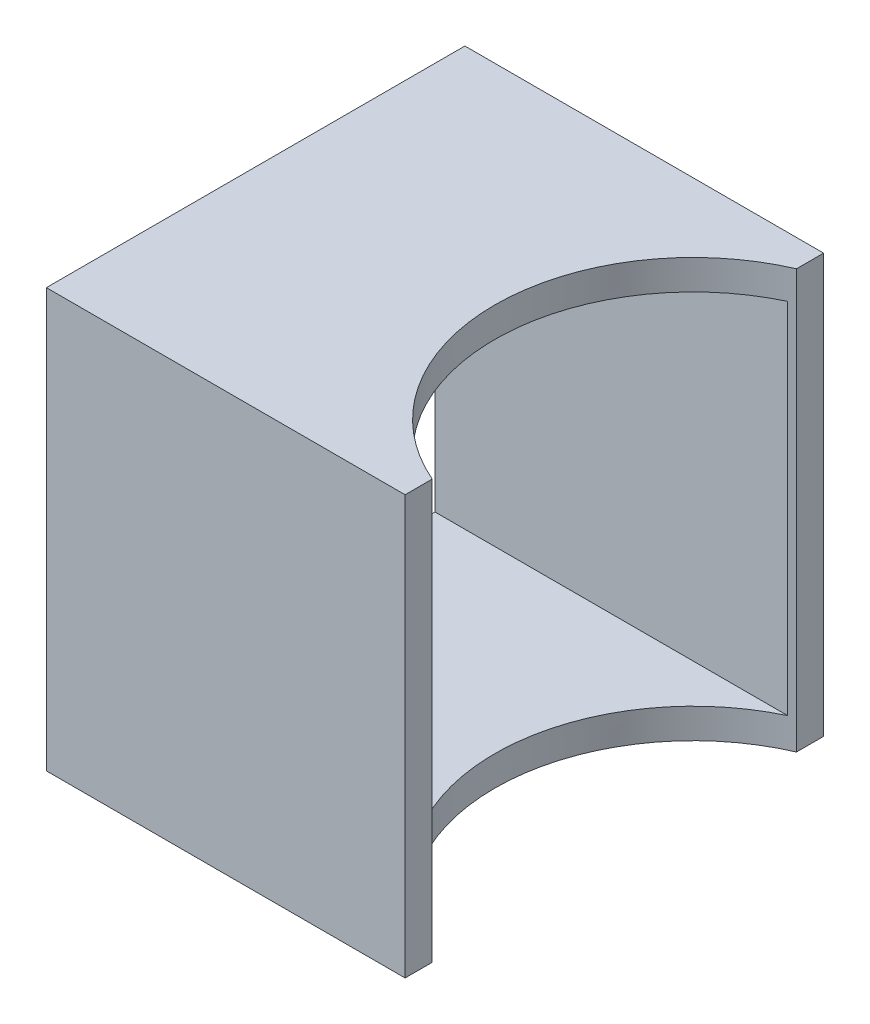
SolidWorks part; units mm, degrees
material "6061 Alloy"
ref_plane "Front Plane" through (0, 0, 0) normal (0, 0, 1) x (1, 0, 0)
ref_plane "Top Plane" through (0, 0, 0) normal (0, 1, 0) x (1, 0, 0)
ref_plane "Right Plane" through (0, 0, 0) normal (1, 0, 0) x (0, 0, -1)
sketch "Sketch1" plane through (0, 0, 0) normal (0, 1, 0) x (1, 0, 0)
  line L0 (0, 0) -> (46.482, 0) construction
  line L1 (0, -22.225) -> (0, 22.225)
  line L2 (0, 22.225) -> (38.1, 22.225)
  line L3 (38.1, 22.225) -> (38.1, 19.3441)
  line L4 (0, -22.225) -> (38.1, -22.225)
  line L5 (38.1, -22.225) -> (38.1, -19.3441)
  circle A0 centre (46.482, 0) radius 21.082
  dimension "D1" = 42.164
  dimension "D2" = 46.482
  dimension "D3" = 44.45
  dimension "D4" = 2.8809
  dimension "D5" = 38.1
extrude "Boss-Extrude1" add sketch "Sketch1" along normal blind 44.45 contours L0 L1 L4 L5 A0 | L1 L0 A0 L3 L2
sketch "Sketch2" plane through (0, 0, 0) normal (-1, 0, 0) x (0, 0, 1)
  line L0 (22.225, 44.45) -> (22.225, 0) construction
  line L1 (-22.225, 44.45) -> (22.225, 44.45) construction
  line L2 (-22.225, 44.45) -> (-22.225, 0) construction
  line L3 (-22.225, 0) -> (22.225, 0) construction
  line L4 (22.225, 44.45) -> (22.225, 0) construction
  line L5 (-19.05, 41.275) -> (-19.05, 3.175)
  line L6 (-19.05, 3.175) -> (19.05, 3.175)
  line L7 (19.05, 41.275) -> (19.05, 3.175)
  line L8 (-19.05, 41.275) -> (19.05, 41.275)
  dimension "D1" = 3.175
extrude "Cut-Extrude1" cut sketch "Sketch2" against normal through all
